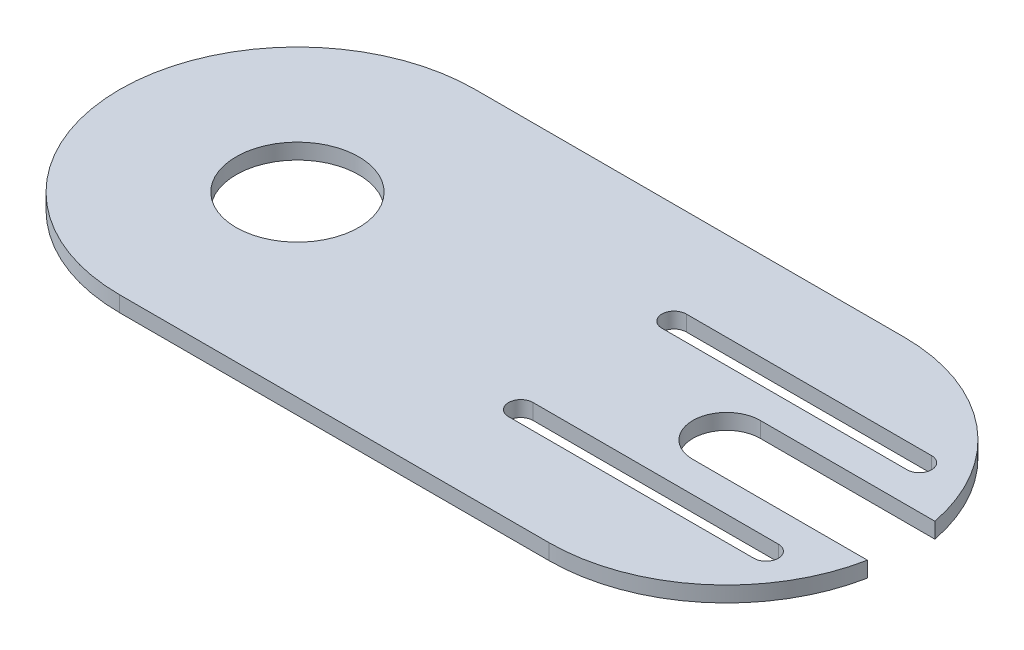
SolidWorks part; units mm, degrees
ref_plane "Front Plane" through (0, 0, 0) normal (0, 0, 1) x (1, 0, 0)
ref_plane "Top Plane" through (0, 0, 0) normal (0, 1, 0) x (1, 0, 0)
ref_plane "Right Plane" through (0, 0, 0) normal (1, 0, 0) x (0, 0, -1)
sketch "Sketch1" plane through (0, 0, 0) normal (0, 1, 0) x (1, 0, 0)
  line L0 (0, 29) -> (70, 29)
  line L1 (0, -29) -> (70, -29)
  line L2 (70, -5.5) -> (98.4737, -5.5)
  line L3 (70, 5.5) -> (98.4737, 5.5)
  line L4 (48.9401, -12.5) -> (96.1677, -12.5) construction
  line L5 (48.9401, -14.5) -> (88.9401, -14.5)
  line L6 (48.9401, -10.5) -> (88.9401, -10.5)
  line L7 (99, 0) -> (75.5, 0) construction
  line L8 (48.9401, 12.5) -> (96.1677, 12.5) construction
  line L9 (48.9401, 10.5) -> (88.9401, 10.5)
  line L10 (48.9401, 14.5) -> (88.9401, 14.5)
  circle A0 centre (0, 0) radius 29
  circle A1 centre (0, 0) radius 10
  arc A2 (70, 29) -> (70, -29) centre (70, 0) cw
  circle A3 centre (70, 0) radius 5.5
  circle A4 centre (48.9401, -12.5) radius 2
  circle A5 centre (88.9401, -12.5) radius 2
  circle A6 centre (88.9401, 12.5) radius 2
  circle A7 centre (48.9401, 12.5) radius 2
  dimension "D1" = 58
  dimension "D2" = 20
  dimension "D4" = 11
  dimension "D6" = 4
  dimension "D3" = 70
  dimension "D5" = 7
  dimension "D7" = 40
extrude "Boss-Extrude1" add sketch "Sketch1" along normal blind 2.54 contours A0 A1 | A3 L3 A2 L0 A0 L1 L2 A5 L5 A4 L6 L9 A7 L10 A6
